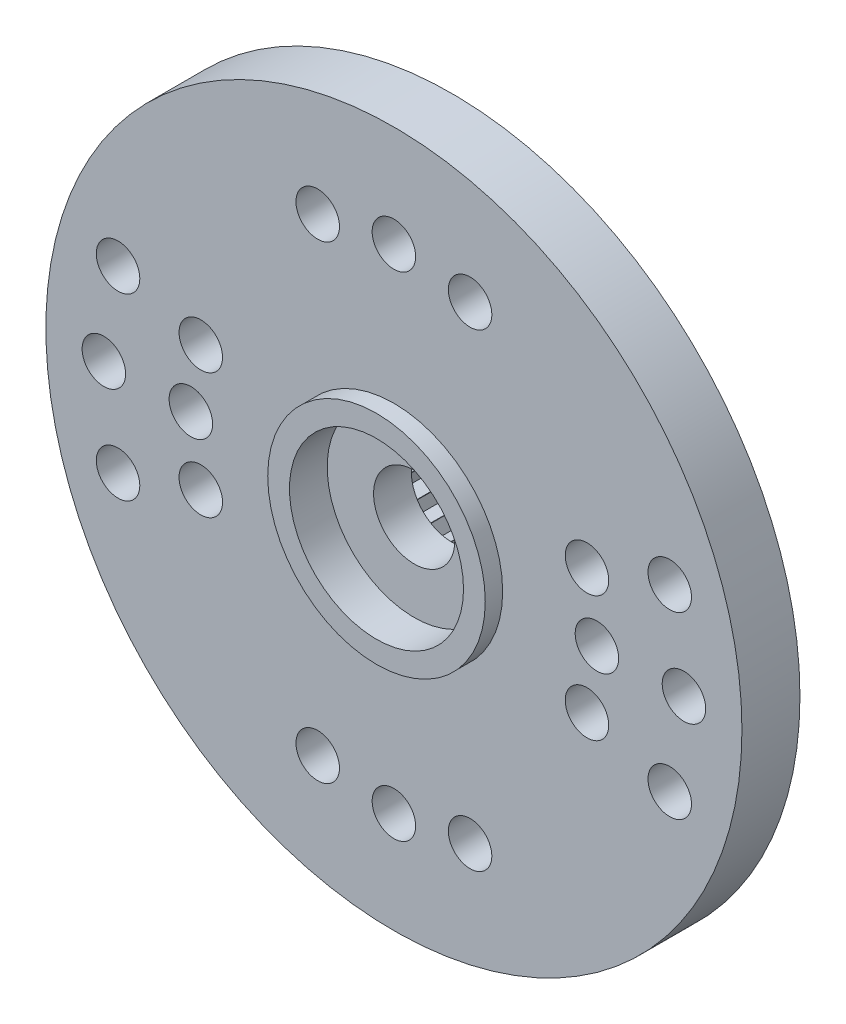
SolidWorks part; units mm, degrees
ref_plane "Face" through (0, 0, 0) normal (0, 0, 1) x (1, 0, 0)
ref_plane "Dessus" through (0, 0, 0) normal (0, 1, 0) x (1, 0, 0)
ref_plane "Droite" through (0, 0, 0) normal (1, 0, 0) x (0, 0, -1)
sketch "Esquisse1" plane through (0, 0, 0) normal (0, 0, 1) x (1, 0, 0)
  circle A0 centre (0, 0) radius 4.5
  line B0 (2.0116, -1.5509) -> (2.0116, -2.0116)
  line B1 (0.3258, 2.519) -> (0, 2.8448)
  line B2 (0.3373, 2.5175) -> (0.3258, 2.519)
  line B3 (0.7363, 2.7479) -> (0.3373, 2.5175)
  line B4 (0.9666, 2.3489) -> (0.7363, 2.7479)
  line B5 (0.9774, 2.3444) -> (0.9666, 2.3489)
  line B6 (1.4224, 2.4637) -> (0.9774, 2.3444)
  line B7 (1.5416, 2.0186) -> (1.4224, 2.4637)
  line B8 (1.5509, 2.0116) -> (1.5416, 2.0186)
  line B9 (2.0116, 2.0116) -> (1.5509, 2.0116)
  line B10 (2.0116, 1.5509) -> (2.0116, 2.0116)
  line B11 (2.0186, 1.5416) -> (2.0116, 1.5509)
  line B12 (2.4637, 1.4224) -> (2.0186, 1.5416)
  line B13 (2.3444, 0.9774) -> (2.4637, 1.4224)
  line B14 (2.3489, 0.9666) -> (2.3444, 0.9774)
  line B15 (2.7479, 0.7363) -> (2.3489, 0.9666)
  line B16 (2.5175, 0.3373) -> (2.7479, 0.7363)
  line B17 (2.519, 0.3258) -> (2.5175, 0.3373)
  line B18 (2.8448, 0) -> (2.519, 0.3258)
  line B19 (2.519, -0.3258) -> (2.8448, 0)
  line B20 (2.5175, -0.3373) -> (2.519, -0.3258)
  line B21 (2.7479, -0.7363) -> (2.5175, -0.3373)
  line B22 (2.3489, -0.9666) -> (2.7479, -0.7363)
  line B23 (2.3444, -0.9774) -> (2.3489, -0.9666)
  line B24 (2.4637, -1.4224) -> (2.3444, -0.9774)
  line B25 (2.0186, -1.5416) -> (2.4637, -1.4224)
  line B26 (2.0116, -1.5509) -> (2.0186, -1.5416)
  line B27 (1.5509, -2.0116) -> (2.0116, -2.0116)
  line B28 (1.5416, -2.0186) -> (1.5509, -2.0116)
  line B29 (1.4224, -2.4637) -> (1.5416, -2.0186)
  line B30 (0.9774, -2.3444) -> (1.4224, -2.4637)
  line B31 (0.9666, -2.3489) -> (0.9774, -2.3444)
  line B32 (0.7363, -2.7479) -> (0.9666, -2.3489)
  line B33 (0.3373, -2.5175) -> (0.7363, -2.7479)
  line B34 (0.3258, -2.519) -> (0.3373, -2.5175)
  line B35 (0, -2.8448) -> (0.3258, -2.519)
  line B36 (-0.3258, -2.519) -> (0, -2.8448)
  line B37 (-0.3373, -2.5175) -> (-0.3258, -2.519)
  line B38 (-0.7363, -2.7479) -> (-0.3373, -2.5175)
  line B39 (-0.9666, -2.3489) -> (-0.7363, -2.7479)
  line B40 (-0.9774, -2.3444) -> (-0.9666, -2.3489)
  line B41 (-1.4224, -2.4637) -> (-0.9774, -2.3444)
  line B42 (-1.5416, -2.0186) -> (-1.4224, -2.4637)
  line B43 (-1.5509, -2.0116) -> (-1.5416, -2.0186)
  line B44 (-2.0116, -2.0116) -> (-1.5509, -2.0116)
  line B45 (-2.0116, -1.5509) -> (-2.0116, -2.0116)
  line B46 (-2.0186, -1.5416) -> (-2.0116, -1.5509)
  line B47 (-2.4637, -1.4224) -> (-2.0186, -1.5416)
  line B48 (-2.3444, -0.9774) -> (-2.4637, -1.4224)
  line B49 (-2.3489, -0.9666) -> (-2.3444, -0.9774)
  line B50 (-2.7479, -0.7363) -> (-2.3489, -0.9666)
  line B51 (-2.5175, -0.3373) -> (-2.7479, -0.7363)
  line B52 (-2.519, -0.3258) -> (-2.5175, -0.3373)
  line B53 (-2.8448, 0) -> (-2.519, -0.3258)
  line B54 (-2.519, 0.3258) -> (-2.8448, 0)
  line B55 (-2.5175, 0.3373) -> (-2.519, 0.3258)
  line B56 (-2.7479, 0.7363) -> (-2.5175, 0.3373)
  line B57 (-2.3489, 0.9666) -> (-2.7479, 0.7363)
  line B58 (-2.3444, 0.9774) -> (-2.3489, 0.9666)
  line B59 (-2.4637, 1.4224) -> (-2.3444, 0.9774)
  line B60 (-2.0186, 1.5416) -> (-2.4637, 1.4224)
  line B61 (-2.0116, 1.5509) -> (-2.0186, 1.5416)
  line B62 (-2.0116, 2.0116) -> (-2.0116, 1.5509)
  line B63 (-1.5509, 2.0116) -> (-2.0116, 2.0116)
  line B64 (-1.5416, 2.0186) -> (-1.5509, 2.0116)
  line B65 (-1.4224, 2.4637) -> (-1.5416, 2.0186)
  line B66 (-0.9774, 2.3444) -> (-1.4224, 2.4637)
  line B67 (-0.9666, 2.3489) -> (-0.9774, 2.3444)
  line B68 (-0.7363, 2.7479) -> (-0.9666, 2.3489)
  line B69 (-0.3373, 2.5175) -> (-0.7363, 2.7479)
  line B70 (-0.3258, 2.519) -> (-0.3373, 2.5175)
  line B71 (0, 2.8448) -> (-0.3258, 2.519)
  dimension "D1" = 9
sketch_block_instance "Block1-1"
sketch_block "Block1"
extrude "Boss.-Extru.1" add sketch "Esquisse1" along normal blind 3
sketch "Esquisse2" plane through (0, 0, 3) normal (0, 0, 1) x (1, 0, 0)
  circle A0 centre (0, 0) radius 12
  circle A1 centre (0, 0) radius 1.4
  dimension "D1" = 24
  dimension "D2" = 2.8
extrude "Boss.-Extru.2" add sketch "Esquisse2" along normal blind 2
sketch "Esquisse3" plane through (0, 0, 5) normal (0, 0, 1) x (1, 0, 0)
  circle A0 centre (0, 0) radius 3.75
  circle A1 centre (0, 0) radius 1.4 construction
  circle A2 centre (0, 0) radius 1.4
  dimension "D1" = 7.5
extrude "Boss.-Extru.3" add sketch "Esquisse3" along normal blind 0.6
sketch "Esquisse4" plane through (0, 0, 5.6) normal (0, 0, 1) x (1, 0, 0)
  circle A0 centre (0, 0) radius 3
  dimension "D1" = 6
extrude "Enlèv. mat.-Extru.1" cut sketch "Esquisse4" against normal blind 1.3
sketch "Esquisse5" plane through (0, 0, 5) normal (0, 0, 1) x (1, 0, 0)
  line L0 (0, 0) -> (-12, 0) construction
  circle A0 centre (0, 0) radius 12 construction
  circle A1 centre (-10, 0) radius 0.75
  circle A2 centre (-7, 0) radius 0.75
  dimension "D1" = 1.5
  dimension "D2" = 10
  dimension "D3" = 3
extrude "Enlèv. mat.-Extru.2" cut sketch "Esquisse5" against normal through all
pattern_circular "Répétition circulaire1" count 20 every 18 about axis through (0, 0, 0) along (0, 0, 1) skipping 2, 3, 4, 5, 6, 7, 8, 12, 13, 14, 15, 16, 17, 18 of "Enlèv. mat.-Extru.2"
sketch "Esquisse6" plane through (0, 0, 5) normal (0, 0, 1) x (1, 0, 0)
  circle A0 centre (0, 8.5) radius 0.75
  dimension "D1" = 1.5
  dimension "D2" = 8.5
extrude "Enlèv. mat.-Extru.3" cut sketch "Esquisse6" against normal through all
pattern_circular "Répétition circulaire2" count 20 every 18 about axis through (0, 0, 0) along (0, 0, 1) skipping 2, 3, 4, 5, 6, 7, 8, 12, 13, 14, 15, 16, 17, 18 of "Enlèv. mat.-Extru.3"
